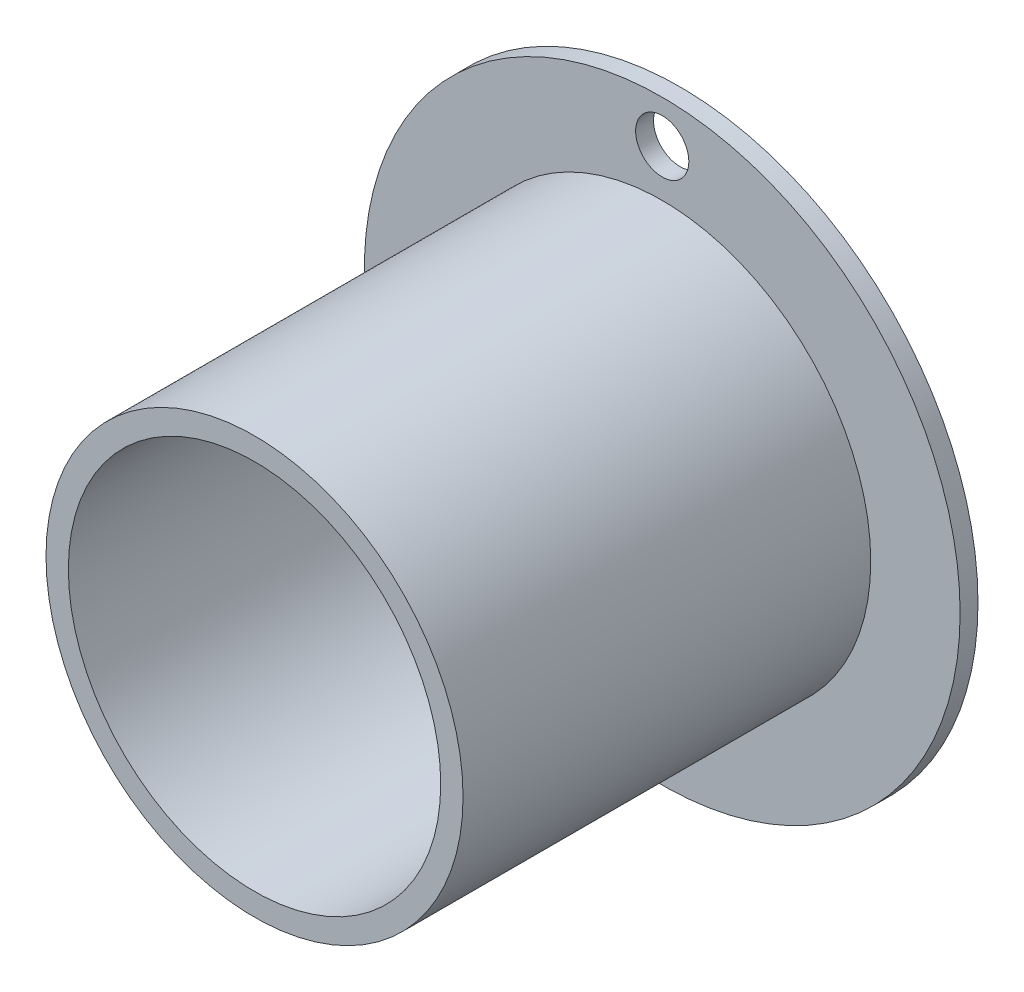
SolidWorks part; units mm, degrees
ref_plane "Front Plane" through (0, 0, 0) normal (0, 0, 1) x (1, 0, 0)
ref_plane "Top Plane" through (0, 0, 0) normal (0, 1, 0) x (1, 0, 0)
ref_plane "Right Plane" through (0, 0, 0) normal (1, 0, 0) x (0, 0, -1)
sketch "Sketch1" plane through (0, 0, 0) normal (0, 0, 1) x (1, 0, 0)
  circle A0 centre (0, 0) radius 17.78
  circle A1 centre (0, 0) radius 11.1125
  dimension "D1" = 35.56
  dimension "D2" = 22.225
extrude "Boss-Extrude1" add sketch "Sketch1" along normal blind 25.4
sketch "Sketch2" plane through (0, 0, 25.4) normal (0, 0, 1) x (1, 0, 0)
  circle A0 centre (0, 0) radius 12.446
  dimension "D1" = 24.892
extrude "Cut-Extrude1" cut sketch "Sketch2" against normal offset from surface 1.0668 and the other way through all from offset 2.54 flip side to cut
hole_wizard "1/8 (0.125) Diameter Hole1" positions "Sketch5" profile "Sketch4" hole size "1/8" standard "ANSI Inch" end condition through all
sketch "Sketch5" plane through (0, 0, 1.0668) normal (0, 0, 1) x (1, 0, 0)
  point P0 (0, 15.24)
  dimension "D1" = 15.24
sketch "Sketch4" plane through (0, 15.24, 1.0668) normal (1, 0, 0) x (0, -1, 0)
  line L0 (0, 0) -> (0, 1.0668)
  line L1 (0, 1.0668) -> (1.5875, 1.0668)
  line L2 (1.5875, 1.0668) -> (1.5875, 0)
  line L5 (1.5875, 0) -> (0, 0)
  line L11 (0, -6.35) -> (0, 107.95) construction
  dimension "Thru Hole Dia." = 3.175
  dimension "Thru Hole Depth" = 1.0668
mirror "Mirror1" about plane through (0, 0, 0) normal (0, 1, 0) of "1/8 (0.125) Diameter Hole1"
